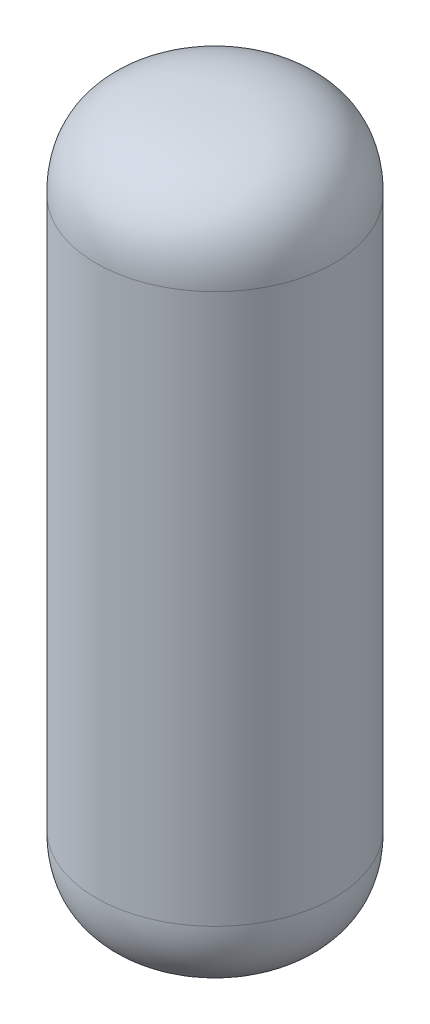
SolidWorks part; units mm, degrees
material "ASTM A106 STEEL GRADE A"
ref_plane "Front Plane" through (0, 0, 0) normal (0, 0, 1) x (1, 0, 0)
ref_plane "Top Plane" through (0, 0, 0) normal (0, 1, 0) x (1, 0, 0)
ref_plane "Right Plane" through (0, 0, 0) normal (1, 0, 0) x (0, 0, -1)
sketch "Sketch1" plane through (0, 0, 0) normal (0, 0, 1) x (1, 0, 0)
  line L0 (0, 0) -> (0, 483) construction
  line L1 (-83.8, 363) -> (-83.8, 60.3811)
  line L2 (0, 0) -> (-62.5853, 0) construction
  line L3 (-78.5716, 363) -> (-78.5716, 398.0129)
  line L4 (-83.8, 363) -> (-83.8, 422.6189)
  line L5 (-83.8, 447.6189) -> (-83.8, 422.6189)
  line L6 (0, 508) -> (0, 505.1767)
  line L7 (-78.5716, 423.0129) -> (-78.5716, 398.0129)
  line L12 (-78.5716, 363) -> (-78.5716, 84.9871)
  line L14 (0, 2.8233) -> (0, 0)
  line L15 (-78.5716, 363) -> (-78.5716, 14.8863) construction
  line L16 (-83.8, 363) -> (-83.8, 15.0605) construction
  line L17 (-66.0394, -3.3031) -> (-62.5853, 0) construction
  line L18 (-68.0431, 2.015) -> (-64.9353, 4.9869) construction
  line L19 (0, 23.9993) -> (-10.0088, 23.9993) construction
  line L20 (0, 29.2277) -> (-10.0088, 29.2277) construction
  arc A8 (-78.5716, 363) -> (-41.9793, 433.7325) centre (8.0871, 363) cw construction
  arc A9 (-83.8, 15.0605) -> (-66.0394, -3.3031) centre (-66.5195, 14.003) ccw construction
  arc A10 (-78.5716, 14.8863) -> (-68.0431, 2.015) centre (-66.5195, 14.003) ccw construction
  arc A11 (-10.0088, 29.2277) -> (-57.8698, 8.3161) centre (-10.0087, -35.9989) ccw construction
  arc A12 (-10.0088, 23.9993) -> (-54.0064, 4.7931) centre (-10.0087, -35.9989) ccw construction
  arc A13 (-62.5853, 0) -> (-54.0064, 4.7931) centre (-65.3295, 14.9857) ccw construction
  arc A14 (-64.9353, 4.9869) -> (-57.8698, 8.3161) centre (-65.3295, 14.9857) ccw construction
  arc A15 (-83.8, 363) -> (-45, 438) centre (8.0871, 363) cw construction
  spline S0 degree 3 poles (-78.5716, 84.9871) (-81.609, 48.9445) (-76.6215, 6.7109) (0, 2.8233) knots 0 0 0 0 1 1 1 1
  spline S1 degree 2 poles (-83.8, 60.3811) (-84.5788, -1.3957) (0, 0) knots 0 0 0 1 1 1
  spline S4 degree 2 poles (-83.8, 447.6189) (-84.5788, 509.3957) (0, 508) knots 0 0 0 1 1 1
  spline S5 degree 3 poles (-78.5716, 423.0129) (-81.609, 459.0555) (-76.6215, 501.2891) (0, 505.1767) knots 0 0 0 0 1 1 1 1
  point P45 (0, 254)
  dimension "D3" = 254
  dimension "D2" = 167.6
  dimension "D7" = 363
revolve "Revolve1" add sketch "Sketch1" angle 360 about L0
